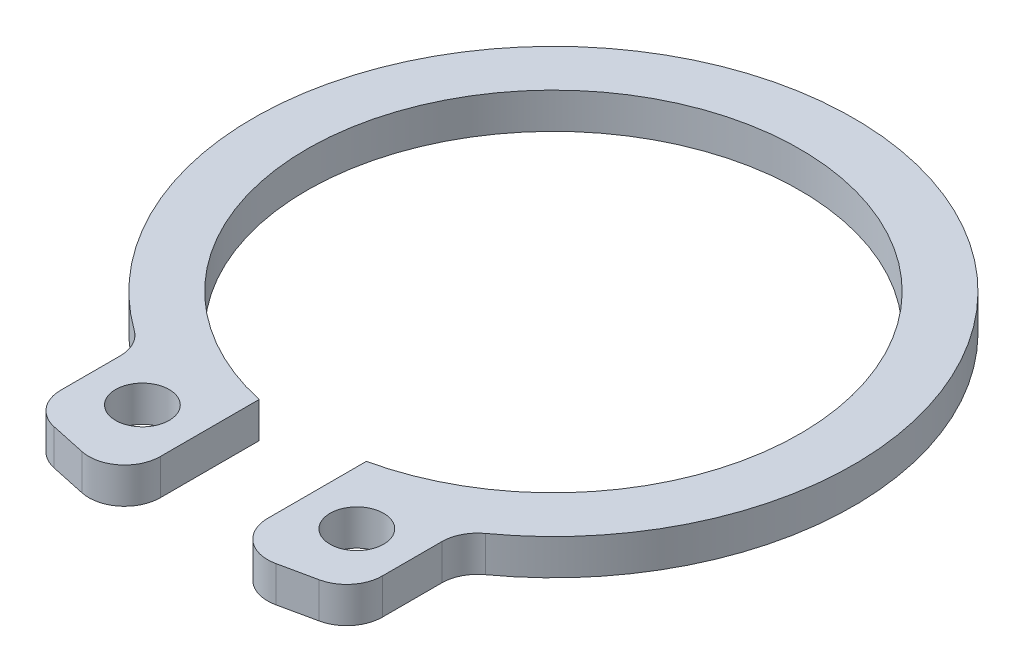
SolidWorks part; units mm, degrees
material "AISI 304"
ref_plane "前视基准面" through (0, 0, 0) normal (0, 0, 1) x (1, 0, 0)
ref_plane "上视基准面" through (0, 0, 0) normal (0, 1, 0) x (1, 0, 0)
ref_plane "右视基准面" through (0, 0, 0) normal (1, 0, 0) x (0, 0, -1)
sketch "草图1" plane through (0, 0, 0) normal (0, 1, 0) x (1, 0, 0)
  line L0 (0, 2.8972) -> (0, -13.1618) construction
  line L1 (-4.5, -7.093) -> (-4.5, -10.093)
  line L2 (-4.5, -10.093) -> (-1.5, -10.735)
  line L3 (-1.5, -10.735) -> (-1.5, -6.735)
  line L4 (1.5, -10.735) -> (1.5, -6.735)
  line L5 (4.5, -10.093) -> (1.5, -10.735)
  line L6 (4.5, -7.093) -> (4.5, -10.093)
  arc A0 (1.5, -6.735) -> (-1.5, -6.735) centre (0, 0) ccw
  arc A1 (4.5, -7.093) -> (-4.5, -7.093) centre (0, 0) ccw
  dimension "D1" = 13.8
  dimension "D2" = 16.8
  dimension "D3" = 1.5
  dimension "D4" = 3
  dimension "D5" = 4
  dimension "D6" = 3
extrude "凸台-拉伸1" add sketch "草图1" along normal blind 1
sketch "草图2" plane through (0, 1, 0) normal (0, 1, 0) x (1, 0, 0)
  line L0 (0, 2.9924) -> (0, -11.4196) construction
  circle A0 centre (-3, -8.5) radius 0.75
  circle A1 centre (3, -8.5) radius 0.75
  dimension "D1" = 1.5
  dimension "D2" = 3
  dimension "D3" = 8.5
extrude "切除-拉伸1" cut sketch "草图2" against normal through all
fillet "圆角1" radius 1 6 edges at (4.5, 0.5, 7.093) (4.5, 0.5, 10.093) (1.5, 0.5, 10.735) (-1.5, 0.5, 10.735) (-4.5, 0.5, 10.093) (-4.5, 0.5, 7.093)
